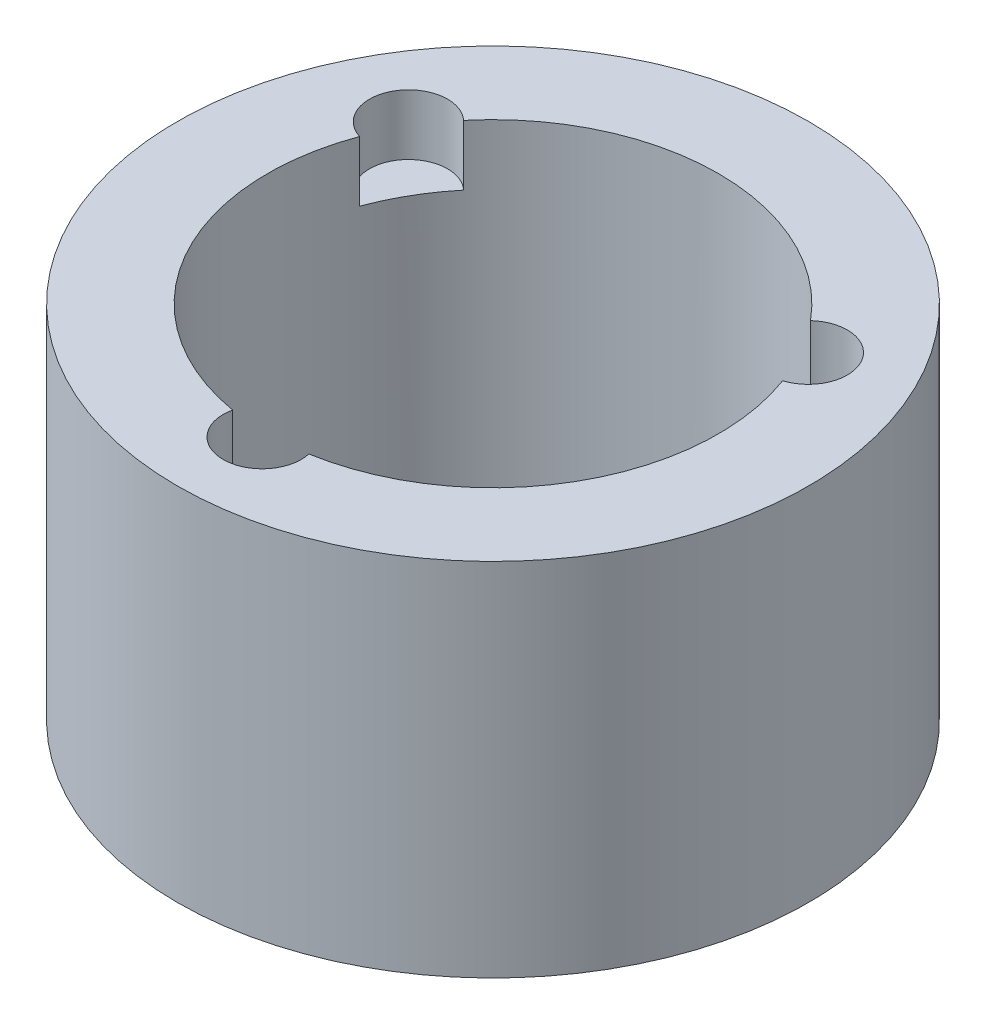
SolidWorks part; units mm, degrees
ref_plane "Front Plane" through (0, 0, 0) normal (0, 0, 1) x (1, 0, 0)
ref_plane "Top Plane" through (0, 0, 0) normal (0, 1, 0) x (1, 0, 0)
ref_plane "Right Plane" through (0, 0, 0) normal (1, 0, 0) x (0, 0, -1)
sketch "Sketch1" plane through (0, 0, 0) normal (0, 1, 0) x (1, 0, 0)
  circle A0 centre (0, 0) radius 44.45
  circle A1 centre (0, 0) radius 31.75
  dimension "D1" = 88.9
  dimension "D2" = 12.7
extrude "Boss-Extrude1" add sketch "Sketch1" along normal blind 50.8
sketch "Sketch3" plane through (0, 50.8, 0) normal (0, 1, 0) x (1, 0, 0)
  line L0 (0, 0) -> (0, -32.5) construction
  line L2 (28.1458, 16.25) -> (0, 0) construction
  line L3 (0, 0) -> (-28.1458, 16.25) construction
  circle A0 centre (0, 0) radius 32.5 construction
  circle A1 centre (-28.1458, 16.25) radius 5.5
  circle A2 centre (0, -32.5) radius 5.5
  circle A3 centre (28.1458, 16.25) radius 5.5
  dimension "D3" = 65
  dimension "D4" = 11
  dimension "D1" = 120
  dimension "D2" = 120
extrude "Cut-Extrude2" cut sketch "Sketch3" against normal blind 8.5
